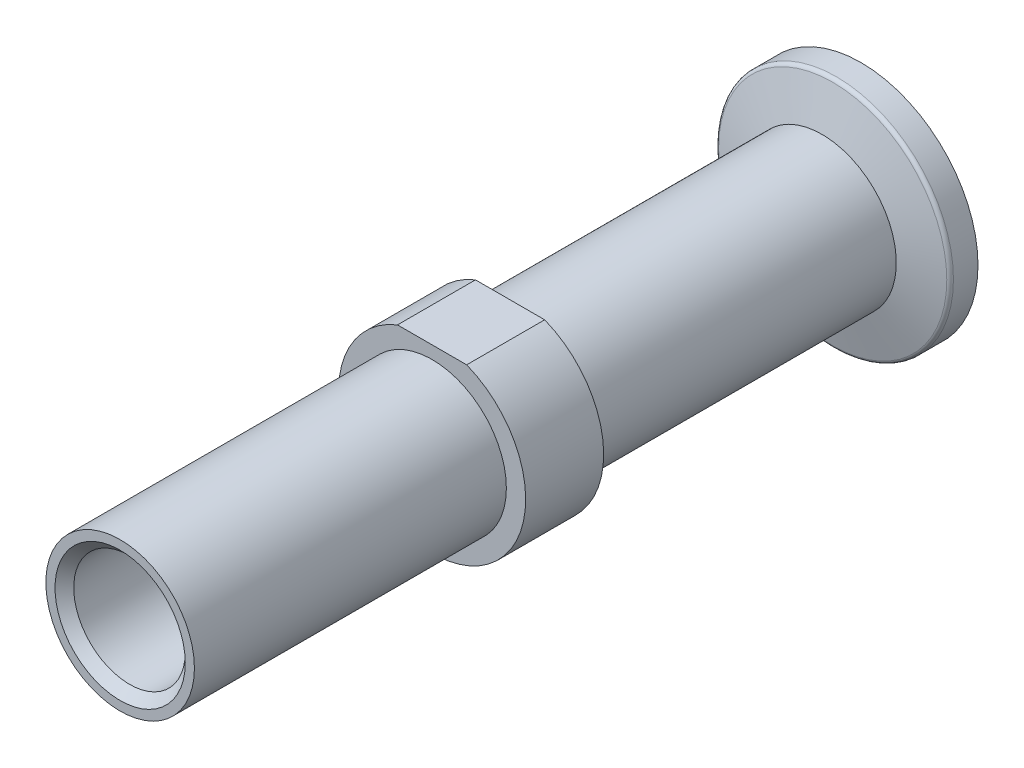
SolidWorks part; units mm, degrees
ref_plane "Front Plane" through (0, 0, 0) normal (0, 0, 1) x (1, 0, 0)
ref_plane "Top Plane" through (0, 0, 0) normal (0, 1, 0) x (1, 0, 0)
ref_plane "Right Plane" through (0, 0, 0) normal (1, 0, 0) x (0, 0, -1)
sketch "Sketch1" plane through (0, 0, 0) normal (0, 0, 1) x (1, 0, 0)
  circle A0 centre (0, 0) radius 12
  dimension "D1" = 24
extrude "Boss-Extrude1" add sketch "Sketch1" along normal blind 90
sketch "Sketch3" plane through (0, 0, 90) normal (0, 0, 1) x (1, 0, 0)
  circle A0 centre (0, 0) radius 9.525
  dimension "D1" = 19.05
extrude "Cut-Extrude1" cut sketch "Sketch3" against normal blind 40 flip side to cut
sketch "Sketch4" plane through (0, 0, 0) normal (0, 0, -1) x (-1, 0, 0)
  circle A0 centre (0, 0) radius 9.525
  dimension "D1" = 19.05
extrude "Cut-Extrude2" cut sketch "Sketch4" against normal blind 40 flip side to cut
sketch "Sketch6" plane through (0, 0, 90) normal (0, 0, 1) x (1, 0, 0)
  circle A0 centre (0, 0) radius 7.15
  dimension "D1" = 14.3
extrude "Cut-Extrude3" cut sketch "Sketch6" against normal through all contours A0
chamfer "Chamfer1" distance 1.2 1 edges at (7.15, 0, 90)
sketch "Sketch7" plane through (0, 0, 0) normal (0, 0, -1) x (-1, 0, 0)
  line L0 (0, 7.15) -> (0, 11.15) construction
  line L1 (0, 11.15) -> (-4.4359, 11.15)
  line L2 (0, 11.15) -> (4.4359, 11.15)
  line L3 (-4.4359, 11.15) -> (-4.4359, 13.873)
  line L4 (-4.4359, 13.873) -> (4.4359, 13.873)
  line L5 (4.4359, 13.873) -> (4.4359, 11.15)
  circle A1 centre (0, 0) radius 7.15 construction
  circle A2 centre (0, 0) radius 12 construction
  dimension "D1" = 4
extrude "Cut-Extrude4" cut sketch "Sketch7" against normal through all
sketch "Sketch8" plane through (0, 11.15, 0) normal (0, 1, 0) x (1, 0, 0)
  circle A0 centre (0, -45.0332) radius 3
  dimension "D1" = 6
extrude "Cut-Extrude5" [suppressed] cut sketch "Sketch8" against normal up to surface (4 mm away)
thread "Thread1" [suppressed] pitch 1 start angle 0, offset 0, length 10, pitch 1, diameter 6
ref_plane "Plane1" through (-3, 11.15, 45.0332) normal (0, 0, 1) x (-1, 0, 0)
sketch "Thread Profile1" plane through (-3, 11.15, 45.0332) normal (0, 0, 1) x (-1, 0, 0)
  line L0 (0, 0) -> (0, 1) construction
  line L1 (0, 0) -> (0.5413, 0.3125)
  line L2 (0.5413, 0.3125) -> (0.5413, 0.4375)
  line L3 (0.5413, 0.4375) -> (0, 0.75)
  line L4 (0.5413, 0.375) -> (0, 0.375) construction
  line L11 (0, 0) -> (0, 0.75)
  point P2 (0, 0)
  dimension "Pitch" = 1
  dimension "Profile_Angle" = 60
  dimension "Profile_Land" = 0.125
  dimension "Profile_Height" = 0.5413
sketch "Sketch10" plane through (0, 0, 0) normal (0, 1, 0) x (1, 0, 0)
  line L13 (0, -1.6) -> (0, 6.3045) construction
  line L15 (9.525, 0) -> (14.6294, 1.3677)
  line L16 (9.525, 0) -> (-9.525, 0) construction
  line L17 (15, 1.8507) -> (15, 5)
  line L18 (15, 5) -> (9, 5)
  line L19 (9, 5) -> (9, 2.5)
  line L20 (9, 2.5) -> (7.15, 2.5)
  line L21 (7.15, 2.5) -> (7.15, 0)
  line L22 (7.15, 0) -> (-7.15, 0) construction
  line L23 (7.15, 0) -> (9.525, 0)
  arc A0 (14.6294, 1.3677) -> (15, 1.8507) centre (14.5, 1.8507) ccw
  point P19 (15, 1.467)
  dimension "D1" = 9
  dimension "D7" = 0.5
  dimension "D2" = 2.5
  dimension "D3" = 75
  dimension "D4" = 5
  dimension "D5" = 7.15
  dimension "D6" = 6
revolve "Revolve1" add sketch "Sketch10" angle 360 about L13
